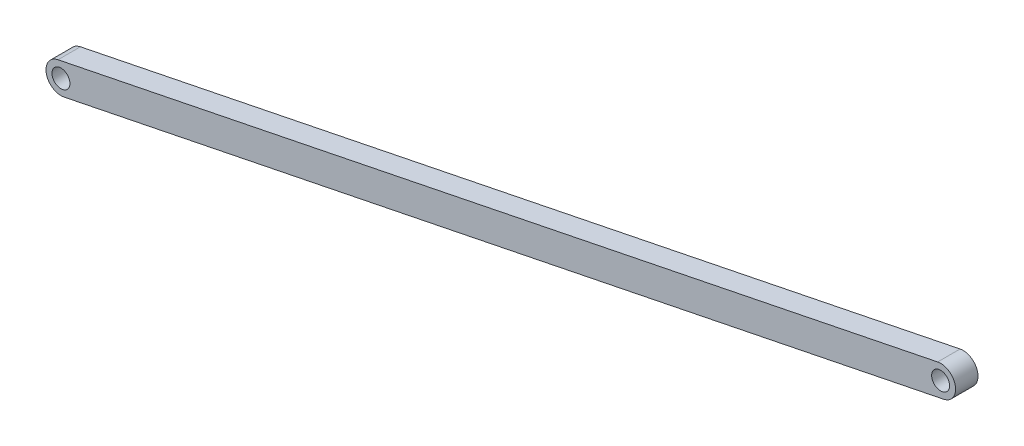
SolidWorks part; units mm, degrees
ref_plane "Front Plane" through (0, 0, 0) normal (0, 0, 1) x (1, 0, 0)
ref_plane "Top Plane" through (0, 0, 0) normal (0, 1, 0) x (1, 0, 0)
ref_plane "Right Plane" through (0, 0, 0) normal (1, 0, 0) x (0, 0, -1)
sketch "Sketch1" plane through (0, 0, 0) normal (0, 0, 1) x (1, 0, 0)
  line L0 (0, 0) -> (1176.1328, 238.142) construction
  line L1 (-3.969, 19.6022) -> (1172.1638, 257.7442)
  line L2 (3.969, -19.6022) -> (1180.1019, 218.5397)
  arc A0 (-3.969, 19.6022) -> (3.969, -19.6022) centre (0, 0) ccw
  arc A1 (1180.1019, 218.5397) -> (1172.1638, 257.7442) centre (1176.1328, 238.142) ccw
  circle A2 centre (0, 0) radius 12
  circle A3 centre (1176.1328, 238.142) radius 12
  point P3 (588.0664, 119.071)
  dimension "D1" = 1200
  dimension "D2" = 24
  dimension "D3" = 40
extrude "Boss-Extrude1" add sketch "Sketch1" along normal blind 30
